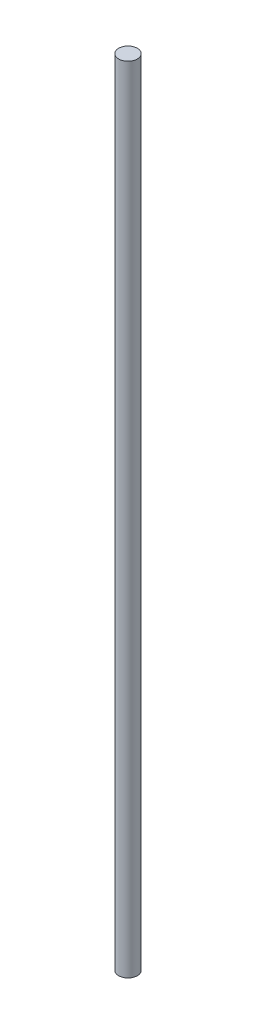
SolidWorks part; units mm, degrees
ref_plane "Alzado" through (0, 0, 0) normal (0, 0, 1) x (1, 0, 0)
ref_plane "Planta" through (0, 0, 0) normal (0, 1, 0) x (1, 0, 0)
ref_plane "Vista lateral" through (0, 0, 0) normal (1, 0, 0) x (0, 0, -1)
sketch "Croquis1" plane through (0, 0, 0) normal (0, 1, 0) x (1, 0, 0)
  circle A0 centre (0, 0) radius 6.35
  dimension "D1" = 12.7
sketch "Croquis2" plane through (0, 0, 0) normal (0, 0, 1) x (1, 0, 0)
  line L0 (0, 0) -> (0, 540)
  dimension "D1" = 540
sweep "Barrer1" add profiles "Croquis1" path "Croquis2"
